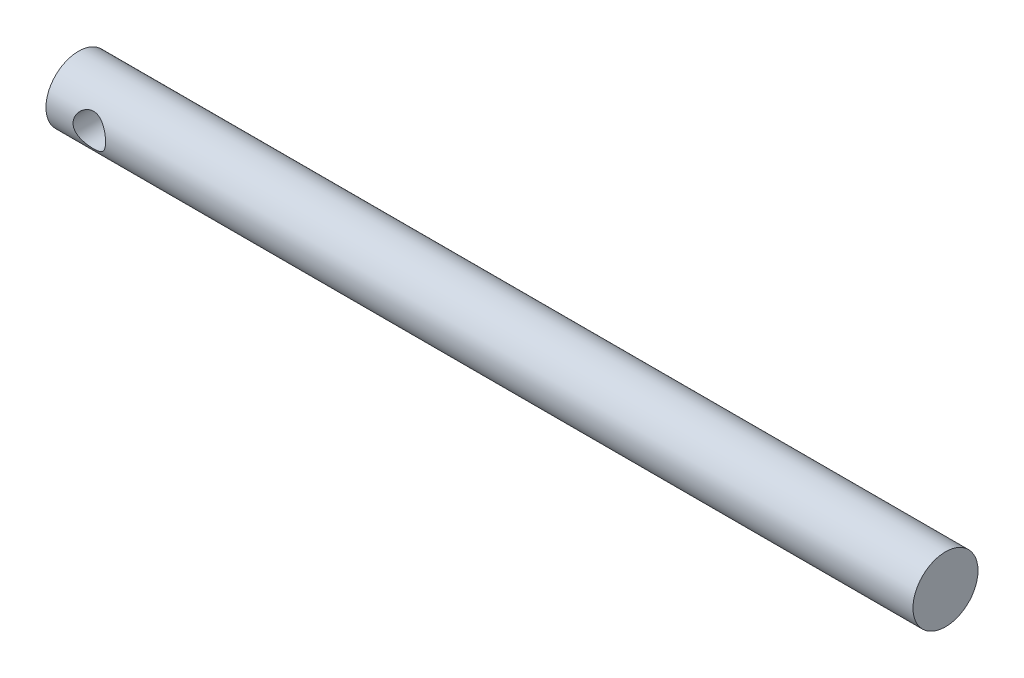
SolidWorks part; units mm, degrees
ref_plane "前基準面" through (0, 0, 0) normal (0, 0, 1) x (1, 0, 0)
ref_plane "上基準面" through (0, 0, 0) normal (0, 1, 0) x (1, 0, 0)
ref_plane "右基準面" through (0, 0, 0) normal (1, 0, 0) x (0, 0, -1)
sketch "草圖1" plane through (0, 0, 0) normal (1, 0, 0) x (0, 0, -1)
  circle A0 centre (0, 0) radius 3
  dimension "D1" = 6
extrude "填料-伸長1" add sketch "草圖1" along normal mid plane 80
sketch "草圖2" plane through (0, 0, 0) normal (0, 0, 1) x (1, 0, 0)
  line L0 (-40, 3) -> (-40, -3) construction
  circle A0 centre (-36, 0) radius 1.5
  point P5 (0, 0)
  dimension "D1" = 4
  dimension "D2" = 3
extrude "除料-伸長1" cut sketch "草圖2" against normal through all both and the other way through all
